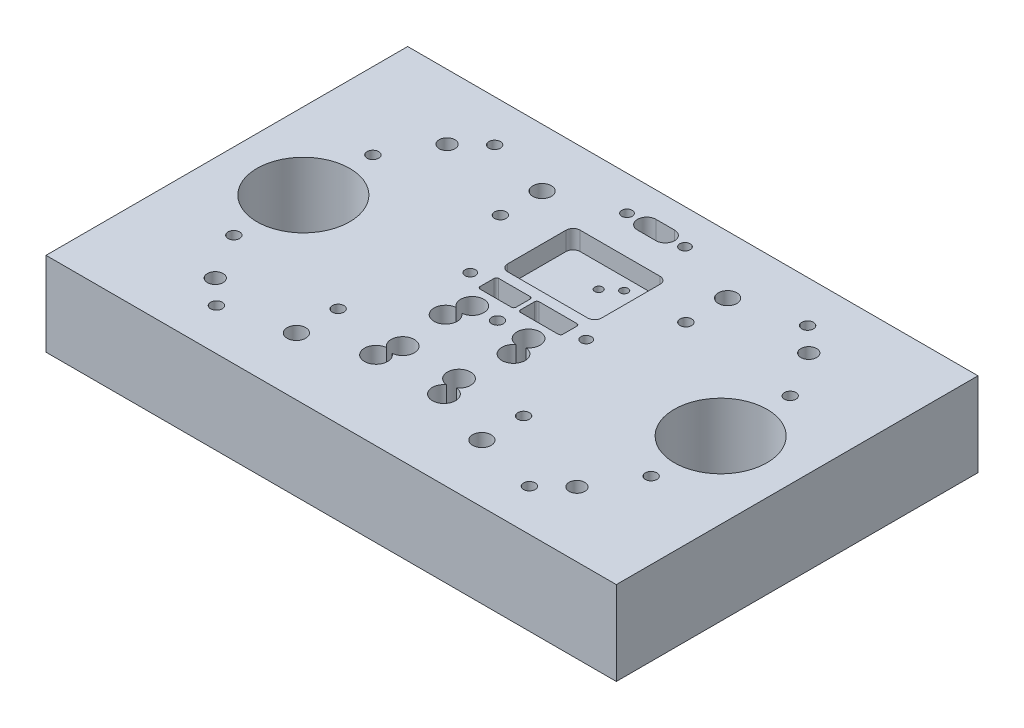
SolidWorks part; units mm, degrees
ref_plane "Front" through (0, 0, 0) normal (0, 0, 1) x (1, 0, 0)
ref_plane "Top" through (0, 0, 0) normal (0, 1, 0) x (1, 0, 0)
ref_plane "Right" through (0, 0, 0) normal (1, 0, 0) x (0, 0, -1)
sketch "Sketch1" plane through (0, 0, 0) normal (0, 0, 1) x (1, 0, 0)
  line L1 (-123, 0) -> (123, 0)
  line L2 (-123, 0) -> (-123, 36.2)
  line L3 (-123, 36.2) -> (123, 36.2)
  line L4 (123, 0) -> (123, 36.2)
  dimension "D1" = 246
  dimension "D2" = 36.2
extrude "Extrude1" add sketch "Sketch1" along normal mid plane 156
hole_wizard "Hole3" positions "Sketch10" profile "Sketch9" legacy end condition through all
sketch "Sketch10" plane through (0, 0, 0) normal (0, -1, 0) x (1, 0, 0)
  line L0 (0, 0) -> (0, -12.6123) construction
  point P0 (90, 0)
  dimension "D1" = 180
sketch "Sketch9" plane through (90, 0, 0) normal (1, 0, 0) x (0, 0, -1)
  line L0 (0, 0) -> (0, 36.2)
  line L1 (0, 36.2) -> (20, 36.2)
  line L2 (20, 36.2) -> (20, 0)
  line L3 (20, 0) -> (0, 0)
  line L4 (0, 110) -> (0, -10) construction
  dimension "Diameter" = 40
  dimension "Depth" = 36.2
pattern_linear "LPattern1" count 2 spacing 180 along (-1, 0, 0) of "Hole3"
chamfer "Chamfer1" [suppressed] distance 1 angle 45
hole_wizard "M6 Tapped Hole1" positions "Sketch12" profile "Sketch11" tap size "M6" standard "ISO" end condition through all
sketch "Sketch12" plane through (0, 36.2, 0) normal (0, 1, 0) x (-1, 0, 0)
  point P4 (-40, 35)
  point P13 (40, 35)
  point P16 (40, -35)
  point P19 (-40, -35)
sketch "Sketch11" plane through (40, 36.2, 35) normal (1, 0, 0) x (0, 0, 1)
  line L0 (0, 0) -> (0, 36.2)
  line L1 (0, 36.2) -> (2.5, 36.2)
  line L2 (2.5, 36.2) -> (2.5, 0)
  line L5 (2.5, 0) -> (0, 0)
  line L11 (0, -6.35) -> (0, 107.95) construction
  dimension "Thru Tap Drill Dia." = 5
  dimension "Thru Tap Drill Depth" = 36.2
cosmetic thread "Hole Thread13" parameters "D1"=36.2, "D2"=6
cosmetic thread "Hole Thread14" parameters "D1"=36.2, "D2"=6
cosmetic thread "Hole Thread15" parameters "D1"=36.2, "D2"=6
cosmetic thread "Hole Thread16" parameters "D1"=36.2, "D2"=6
hole_wizard "Hole4" positions "Sketch14" profile "Sketch13" legacy end condition through all
sketch "Sketch14" plane through (0, 36.2, 0) normal (0, 1, 0) x (-1, 0, 0)
  point P1 (-40, -53)
  point P4 (-40, 53)
  point P7 (40, 53)
  point P10 (40, -53)
sketch "Sketch13" plane through (40, 36.2, -53) normal (1, 0, 0) x (0, 0, 1)
  line L0 (0, 0) -> (0, 36.2)
  line L1 (0, 36.2) -> (4, 36.2)
  line L2 (4, 36.2) -> (4, 0)
  line L3 (4, 0) -> (0, 0)
  line L4 (0, 110) -> (0, -10) construction
  dimension "Diameter" = 8
  dimension "Depth" = 36.2
hole_wizard "M8 Tapped Hole1" positions "Sketch16" profile "Sketch15" tap size "M8" standard "ISO" end condition through all
sketch "Sketch16" plane through (0, 36.2, 0) normal (0, 1, 0) x (-1, 0, 0)
  point P0 (78, 50)
  dimension "D1" = 78
  dimension "D2" = 50
sketch "Sketch15" plane through (-78, 36.2, 50) normal (1, 0, 0) x (0, 0, 1)
  line L0 (0, 0) -> (0, 36.2)
  line L1 (0, 36.2) -> (3.4, 36.2)
  line L2 (3.4, 36.2) -> (3.4, 0)
  line L5 (3.4, 0) -> (0, 0)
  line L11 (0, -6.35) -> (0, 107.95) construction
  dimension "Thru Tap Drill Dia." = 6.8
  dimension "Thru Tap Drill Depth" = 36.2
cosmetic thread "Hole Thread7" parameters "D2"=8
pattern_linear "LPattern2" count 2 spacing 100 along (0, 0, -1) count 2 spacing 156 along (1, 0, 0) of "M8 Tapped Hole1"
hole_wizard "M6 Tapped Hole2" positions "Sketch18" profile "Sketch19" tap size "M6" standard "ISO" end condition through all
sketch "Sketch18" plane through (0, 36.2, 0) normal (0, 1, 0) x (-1, 0, 0)
  line L0 (90, 0) -> (90, -30) construction
  line L1 (90, 0) -> (90, 30) construction
  line L2 (0, 0) -> (0, -12.6901) construction
  point P0 (90, 30)
  point P1 (90, -30)
  point P18 (-90, -30)
  point P19 (-90, 30)
  dimension "D1" = 60
sketch "Sketch19" plane through (-90, 36.2, 30) normal (1, 0, 0) x (0, 0, 1)
  line L0 (0, 0) -> (0, 36.2)
  line L1 (0, 36.2) -> (2.5, 36.2)
  line L2 (2.5, 36.2) -> (2.5, 0)
  line L5 (2.5, 0) -> (0, 0)
  line L11 (0, -6.35) -> (0, 107.95) construction
  dimension "Thru Tap Drill Dia." = 5
  dimension "Thru Tap Drill Depth" = 36.2
cosmetic thread "Hole Thread8" parameters "D2"=6
cosmetic thread "Hole Thread9" parameters "D2"=6
cosmetic thread "Hole Thread10" parameters "D2"=6
cosmetic thread "Hole Thread11" parameters "D2"=6
hole_wizard "M6 Tapped Hole3" positions "Sketch27" profile "Sketch26" tap size "M6" standard "ISO" end condition through all
sketch "Sketch27" plane through (0, 36.2, 0) normal (0, 1, 0) x (-1, 0, 0)
  point P0 (67.5, -60)
  dimension "D1" = 67.5
  dimension "D2" = 60
sketch "Sketch26" plane through (-67.5, 36.2, -60) normal (1, 0, 0) x (0, 0, 1)
  line L0 (0, 0) -> (0, 36.2)
  line L1 (0, 36.2) -> (2.5, 36.2)
  line L2 (2.5, 36.2) -> (2.5, 0)
  line L5 (2.5, 0) -> (0, 0)
  line L11 (0, -6.35) -> (0, 107.95) construction
  dimension "Thru Tap Drill Dia." = 5
  dimension "Thru Tap Drill Depth" = 36.2
cosmetic thread "Hole Thread12" parameters "D2"=6
pattern_linear "LPattern3" count 2 spacing 135 along (1, 0, 0) count 2 spacing 120 along (0, 0, 1) of "M6 Tapped Hole3"
hole_wizard "Hole6" positions "Sketch29" profile "Sketch28" legacy
sketch "Sketch29" plane through (0, 36.2, 0) normal (0, 1, 0) x (-1, 0, 0)
  point P1 (-12.15, 35)
  point P4 (12.15, 35)
  point P7 (-12.15, 5)
  point P10 (12.15, 5)
  point P13 (14.65, 14)
  point P16 (-14.65, 14)
  point P19 (-14.65, 44)
  point P22 (14.65, 44)
sketch "Sketch28" plane through (12.15, 36.2, 35) normal (1, 0, 0) x (0, 0, 1)
  line L0 (0, 0) -> (0, 25)
  line L1 (0, 25) -> (5, 25)
  line L2 (5, 25) -> (5, 0)
  line L3 (5, 0) -> (0, 0)
  line L4 (0, 110) -> (0, -10) construction
  dimension "Diameter" = 10
  dimension "Depth" = 25
sketch "Sketch30" plane through (0, 36.2, 0) normal (0, 1, 0) x (1, 0, 0)
  line L0 (-0.8954, 64.19) -> (-0.8954, 61.81) construction
  line L4 (3.1046, 63) -> (-4.8954, 63) construction
  line L5 (3.1046, 59) -> (-4.8954, 59)
  line L6 (3.1046, 67) -> (-4.8954, 67)
  line L7 (0.1966, 8.05) -> (0.1966, 5.95) construction
  line L8 (16.96, 11.01) -> (0.6966, 11.01)
  line L9 (17.96, 10.01) -> (17.96, 3.99)
  line L10 (16.96, 2.99) -> (0.6966, 2.99)
  line L11 (-0.3034, 10.01) -> (-0.3034, 3.99)
  line L12 (-3.2354, 11.01) -> (-16.7354, 11.01)
  line L13 (-2.2354, 10.01) -> (-2.2354, 3.99)
  line L14 (-3.2354, 2.99) -> (-16.7354, 2.99)
  line L15 (-17.7354, 10.01) -> (-17.7354, 3.99)
  line L16 (-2.7354, 5.94) -> (-2.7354, 8.06) construction
  line L17 (17.15, 10.01) -> (9.65, 10.01) construction
  line L18 (9.65, 3.99) -> (17.15, 3.99) construction
  line L19 (17.46, 4.3) -> (17.46, 9.7) construction
  line L20 (-17.2354, 9.7) -> (-17.2354, 4.3) construction
  arc A0 (3.1046, 59) -> (3.1046, 67) centre (3.1046, 63) ccw
  arc A1 (-1.0214, 64.232) -> (-0.7694, 64.232) centre (-0.8954, 64.4) ccw construction
  arc A2 (-0.7694, 61.768) -> (-1.0214, 61.768) centre (-0.8954, 61.6) ccw construction
  arc A3 (-4.8954, 67) -> (-4.8954, 59) centre (-4.8954, 63) ccw
  circle A4 centre (-1.2694, -5) radius 2.5
  arc A5 (-16.7354, 2.99) -> (-17.7354, 3.99) centre (-16.7354, 3.99) cw
  arc A6 (-16.7354, 11.01) -> (-17.7354, 10.01) centre (-16.7354, 10.01) ccw
  arc A7 (-3.2354, 11.01) -> (-2.2354, 10.01) centre (-3.2354, 10.01) cw
  arc A8 (-2.2354, 3.99) -> (-3.2354, 2.99) centre (-3.2354, 3.99) cw
  arc A9 (17.96, 3.99) -> (16.96, 2.99) centre (16.96, 3.99) cw
  arc A10 (16.96, 11.01) -> (17.96, 10.01) centre (16.96, 10.01) cw
  arc A11 (0.6966, 11.01) -> (-0.3034, 10.01) centre (0.6966, 10.01) ccw
  arc A12 (0.6966, 2.99) -> (-0.3034, 3.99) centre (0.6966, 3.99) cw
  point P10 (-0.8954, 63)
  dimension "D1" = 8
  dimension "D3" = 5
  dimension "D10" = 1
  dimension "D2" = 8
  dimension "D4" = 0.5
  dimension "D5" = 0.5
  dimension "D6" = 1.9319
  dimension "D7" = 1
  dimension "D8" = 1
  dimension "D9" = 0.5
  dimension "D11" = 0.5
extrude "Cut-Extrude1" cut sketch "Sketch30" against normal through all
sketch "Sketch31" plane through (0, 0, 0) normal (0, -1, 0) x (1, 0, 0)
  circle A0 centre (-1.2694, 5) radius 5
  dimension "D1" = 10
extrude "Cut-Extrude2" cut sketch "Sketch31" against normal offset from surface (24.2 mm away) 12 up to face at (8.8283, 36.2, -7)
hole_wizard "CBORE for M3 Hex Socket Head Cap Screw1" positions "Sketch33" profile "Sketch32" counterbore size "M3" standard "ISO" end condition through all
sketch "Sketch33" plane through (0, 0, 0) normal (0, -1, 0) x (1, 0, 0)
  point P0 (-12.1954, -21)
  point P3 (12.4, -21)
  point P6 (0.9046, -36.5)
  point P9 (6.9046, -41.5)
sketch "Sketch32" plane through (-12.1954, 0, -21) normal (1, 0, 0) x (0, 0, -1)
  line L0 (0, 0) -> (0, 36.2)
  line L1 (0, 36.2) -> (1.7, 36.2)
  line L3 (1.7, 36.2) -> (1.7, 6.4)
  line L4 (1.7, 6.4) -> (3.25, 6.4)
  line L5 (3.25, 6.4) -> (3.25, 0)
  line L7 (3.25, 0) -> (0, 0)
  line L11 (0, -6.35) -> (0, 107.95) construction
  dimension "Thru Hole Dia." = 3.4
  dimension "Thru Hole Depth" = 36.2
  dimension "C'Bore Dia." = 6.5
  dimension "C'Bore Depth" = 6.4
hole_wizard "CBORE for M4 Hex Socket Head Cap Screw1" positions "Sketch35" profile "Sketch34" counterbore size "M4" standard "ISO" end condition through all
sketch "Sketch35" plane through (0, 0, 0) normal (0, -1, 0) x (1, 0, 0)
  point P0 (-25, -7)
  point P3 (25, -7)
  point P6 (-13.3954, -63)
  point P9 (11.6046, -63)
sketch "Sketch34" plane through (-25, 0, -7) normal (1, 0, 0) x (0, 0, -1)
  line L0 (0, 0) -> (0, 36.2)
  line L1 (0, 36.2) -> (2.25, 36.2)
  line L3 (2.25, 36.2) -> (2.25, 4.4)
  line L4 (2.25, 4.4) -> (4, 4.4)
  line L5 (4, 4.4) -> (4, 0)
  line L7 (4, 0) -> (0, 0)
  line L11 (0, -6.35) -> (0, 107.95) construction
  dimension "Thru Hole Dia." = 4.5
  dimension "Thru Hole Depth" = 36.2
  dimension "C'Bore Dia." = 8
  dimension "C'Bore Depth" = 4.4
sketch "Sketch36" plane through (0, 36.2, 0) normal (0, 1, 0) x (1, 0, 0)
  line L0 (20, 43.35) -> (20, 18.65) construction
  line L1 (17.25, 46.6) -> (-17.25, 46.6)
  line L2 (20.25, 43.6) -> (20.25, 18.4)
  line L3 (17.25, 15.4) -> (-17.25, 15.4)
  line L4 (-20.25, 43.6) -> (-20.25, 18.4)
  line L5 (17, 15.65) -> (-17, 15.65) construction
  line L6 (-20, 18.65) -> (-20, 43.35) construction
  line L7 (-17, 46.35) -> (17, 46.35) construction
  arc A0 (-17.25, 46.6) -> (-20.25, 43.6) centre (-17.25, 43.6) ccw
  arc A1 (-17.25, 15.4) -> (-20.25, 18.4) centre (-17.25, 18.4) cw
  arc A2 (20.25, 18.4) -> (17.25, 15.4) centre (17.25, 18.4) cw
  arc A3 (17.25, 46.6) -> (20.25, 43.6) centre (17.25, 43.6) cw
  dimension "D5" = 3
  dimension "D1" = 0.25
  dimension "D2" = 0.25
  dimension "D3" = 0.25
  dimension "D4" = 0.25
extrude "Cut-Extrude3" cut sketch "Sketch36" against normal blind 8
